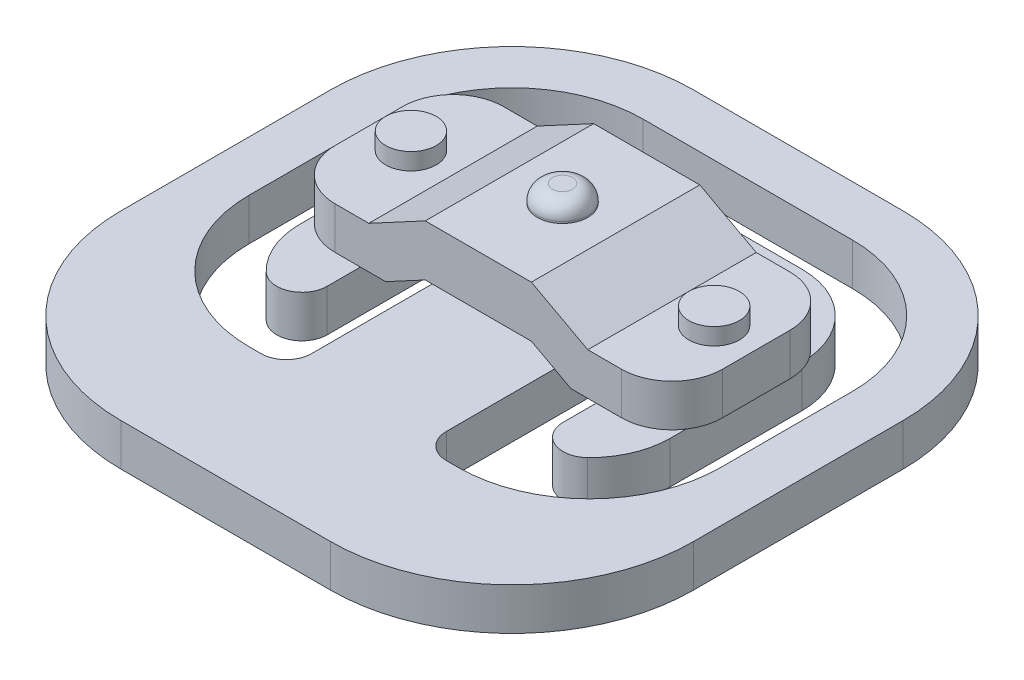
SolidWorks part; units mm, degrees
ref_plane "Front Plane" through (0, 0, 0) normal (0, 0, 1) x (1, 0, 0)
ref_plane "Top Plane" through (0, 0, 0) normal (0, 1, 0) x (1, 0, 0)
ref_plane "Right Plane" through (0, 0, 0) normal (1, 0, 0) x (0, 0, -1)
sketch "Sketch1" plane through (0, 0, 0) normal (0, 1, 0) x (1, 0, 0)
  line L1 (-6.2129, -17) -> (6.2129, -17)
  line L2 (-17, -6.2129) -> (-17, 6.2129)
  line L3 (-6.2129, 17) -> (6.2129, 17)
  line L4 (17, -6.2129) -> (17, 6.2129)
  line L5 (-17, -17) -> (17, 17) construction
  line L6 (-17, 17) -> (17, -17) construction
  arc A0 (6.2129, -17) -> (17, -6.2129) centre (6.2129, -6.2129) ccw
  arc A1 (-6.2129, -17) -> (-17, -6.2129) centre (-6.2129, -6.2129) cw
  arc A2 (-17, 6.2129) -> (-6.2129, 17) centre (-6.2129, 6.2129) cw
  arc A3 (17, 6.2129) -> (6.2129, 17) centre (6.2129, 6.2129) ccw
  point P0 (0, 0)
  dimension "D3" = 10.7871
  dimension "D1" = 34
  dimension "D2" = 34
extrude "Boss-Extrude1" add sketch "Sketch1" along normal blind 2.5
sketch "Sketch2" plane through (0, 2.5, 0) normal (0, 1, 0) x (1, 0, 0)
  line L0 (5.4, 3.7) -> (5.6, 3.7)
  line L1 (5.5, -9.4) -> (6.21, -9.4)
  line L3 (11, -1.61) -> (11, 6.2129)
  line L4 (6.2129, 11) -> (-6.2129, 11)
  line L5 (-11, 6.2129) -> (-11, -1.61)
  line L6 (14, -6.2129) -> (14, 6.2129)
  line L7 (6.2129, 14) -> (-6.2129, 14)
  line L8 (-14, 6.2129) -> (-14, -6.2129)
  line L9 (14, -1.61) -> (14, 6.2129)
  line L10 (6.2129, 14) -> (-6.2129, 14)
  line L11 (-14, 6.2129) -> (-14, -1.61)
  line L12 (-6.21, -9.4) -> (-5.5, -9.4)
  line L13 (-6.2129, -17) -> (6.2129, -17) construction
  line L14 (14, -6.4) -> (14, 6.2129) construction
  line L15 (-14, 6.2129) -> (-14, -6.2129) construction
  line L17 (-11, 6.2129) -> (-11, -6.2129) construction
  line L18 (11, -6.4) -> (11, 6.2129) construction
  line L19 (0, 0) -> (0, -17) construction
  line L20 (-4, -7.9) -> (-4, 2.3)
  line L21 (4, -7.9) -> (4, 2.3)
  line L23 (-5.6, 3.7) -> (-5.4, 3.7)
  line L24 (6.2129, 17) -> (-6.2129, 17) construction
  line L25 (7, -3.9722) -> (7, 2.3)
  line L26 (-7, -3.9722) -> (-7, 2.3)
  arc A0 (-9.5441, -5.0492) -> (-7, -3.9722) centre (-8.5, -3.9722) ccw
  arc A1 (9.5441, -5.0492) -> (7, -3.9722) centre (8.5, -3.9722) cw
  arc A2 (11, 6.2129) -> (6.2129, 11) centre (6.2129, 6.2129) ccw
  arc A3 (-6.2129, 11) -> (-11, 6.2129) centre (-6.2129, 6.2129) ccw
  arc A4 (14, 6.2129) -> (6.2129, 14) centre (6.2129, 6.2129) ccw
  arc A5 (-6.2129, 14) -> (-14, 6.2129) centre (-6.2129, 6.2129) ccw
  arc A6 (14, 6.2129) -> (6.2129, 14) centre (6.2129, 6.2129) ccw
  arc A7 (-6.2129, 14) -> (-14, 6.2129) centre (-6.2129, 6.2129) ccw
  arc A8 (6.21, -9.4) -> (14, -1.61) centre (6.21, -1.61) ccw
  arc A9 (-14, -1.61) -> (-6.21, -9.4) centre (-6.21, -1.61) ccw
  arc A10 (9.5441, -5.0492) -> (11, -1.61) centre (6.21, -1.61) ccw
  arc A11 (-9.5441, -5.0492) -> (-11, -1.61) centre (-6.21, -1.61) cw
  arc A12 (5.5, -9.4) -> (4, -7.9) centre (5.5, -7.9) cw
  arc A13 (-4, -7.9) -> (-5.5, -9.4) centre (-5.5, -7.9) cw
  arc A14 (7, 2.3) -> (5.6, 3.7) centre (5.6, 2.3) ccw
  arc A15 (4, 2.3) -> (5.4, 3.7) centre (5.4, 2.3) cw
  arc A16 (-4, 2.3) -> (-5.4, 3.7) centre (-5.4, 2.3) ccw
  arc A17 (-5.6, 3.7) -> (-7, 2.3) centre (-5.6, 2.3) ccw
  point P56 (7, 3.7)
  point P59 (4, 3.7)
  point P62 (-4, 3.7)
  point P65 (-7, 3.7)
  dimension "D4" = 7.79
  dimension "D6" = 4.79
  dimension "D5" = 1.5
  dimension "D10" = 1.4
  dimension "D3" = 7.6
  dimension "D7" = 4
  dimension "D8" = 3
  dimension "D9" = 13.3
  dimension "D1" = 3
  dimension "D2" = 3
extrude "Cut-Extrude1" cut sketch "Sketch2" against normal through all
sketch "Sketch3" plane through (0, 2.5, 0) normal (0, 1, 0) x (1, 0, 0)
  line L0 (0, 0) -> (0, -17) construction
  line L1 (-8.5, 8) -> (8.5, 8)
  line L2 (-11.5, 5) -> (-11.5, 1)
  line L3 (-8.5, -2) -> (8.5, -2)
  line L4 (11.5, 5) -> (11.5, 1)
  line L5 (-6.2129, -17) -> (6.2129, -17) construction
  line L6 (6.2129, 17) -> (-6.2129, 17) construction
  arc A0 (11.5, 5) -> (8.5, 8) centre (8.5, 5) ccw
  arc A1 (8.5, -2) -> (11.5, 1) centre (8.5, 1) ccw
  arc A2 (-8.5, -2) -> (-11.5, 1) centre (-8.5, 1) cw
  arc A3 (-8.5, 8) -> (-11.5, 5) centre (-8.5, 5) ccw
  point P13 (11.5, 8)
  point P16 (11.5, -2)
  point P19 (-11.5, -2)
  dimension "D5" = 3
  dimension "D1" = 10
  dimension "D2" = 19
  dimension "D3" = 23
  dimension "D4" = 11.5
extrude "Boss-Extrude2" add sketch "Sketch3" along normal blind 4.3
sketch "Sketch4" plane through (0, 0, 2) normal (0, 0, 1) x (1, 0, 0)
  line L0 (-11.5, 5) -> (-6.5, 5)
  line L1 (-11.5, 6.8) -> (-11.5, 2.5) construction
  line L2 (-6.5, 5) -> (-3.15, 6.8)
  line L3 (-8.5, 6.8) -> (8.5, 6.8) construction
  line L4 (0, 2.5) -> (0, 6.8) construction
  line L5 (-4, 2.5) -> (4, 2.5) construction
  line L6 (-8.5, 2.5) -> (-11, 2.5) construction
  line L7 (6.5, 5) -> (3.15, 6.8)
  line L8 (11.5, 5) -> (6.5, 5)
  line L9 (-3.15, 6.8) -> (3.15, 6.8)
  line L10 (11.5, 5) -> (14.6646, 7.6571)
  line L11 (14.6646, 7.6571) -> (13.998, 12.8786)
  line L12 (13.998, 12.8786) -> (-15.8311, 15.2671)
  line L13 (-15.8311, 15.2671) -> (-17.3864, 7.6571)
  line L14 (-17.3864, 7.6571) -> (-11.5, 5)
  line L15 (3.15, 3.7627) -> (-3.15, 3.7627)
  line L16 (-3.15, 3.7627) -> (-5.5, 2.5)
  line L17 (-7, 2.5) -> (-4, 2.5) construction
  line L18 (3.15, 3.7627) -> (5.5, 2.5)
  line L19 (-5.5, 2.5) -> (5.5, 2.5)
  point P29 (0, 3.7627)
  dimension "D1" = 3.15
  dimension "D2" = 5
  dimension "D3" = 2.5
extrude "Cut-Extrude2" cut sketch "Sketch4" against normal through all
sketch "Sketch5" plane through (0, 5, 0) normal (0, 1, 0) x (1, 0, 0)
  line L0 (11.5, 3) -> (6.5, 3) construction
  line L1 (11.5, 5) -> (11.5, 1) construction
  line L2 (6.5, 8) -> (6.5, -2) construction
  circle A0 centre (9, 3) radius 1.5
  dimension "D1" = 3
extrude "Boss-Extrude3" add sketch "Sketch5" along normal blind 1
mirror "Mirror1" about plane through (0, 0, 0) normal (1, 0, 0) of "Boss-Extrude3"
sketch "Sketch6" plane through (0, 6.8, 0) normal (0, 1, 0) x (1, 0, 0)
  line L0 (0, 8) -> (0, -2) construction
  line L1 (3.15, 8) -> (-3.15, 8) construction
  line L2 (-3.15, -2) -> (3.15, -2) construction
  circle A0 centre (0, 3) radius 1.5
  dimension "D1" = 3
extrude "Boss-Extrude4" add sketch "Sketch6" along normal blind 1
fillet "Fillet1" radius 0.9 1 edges at (0, 7.8, -1.5)
